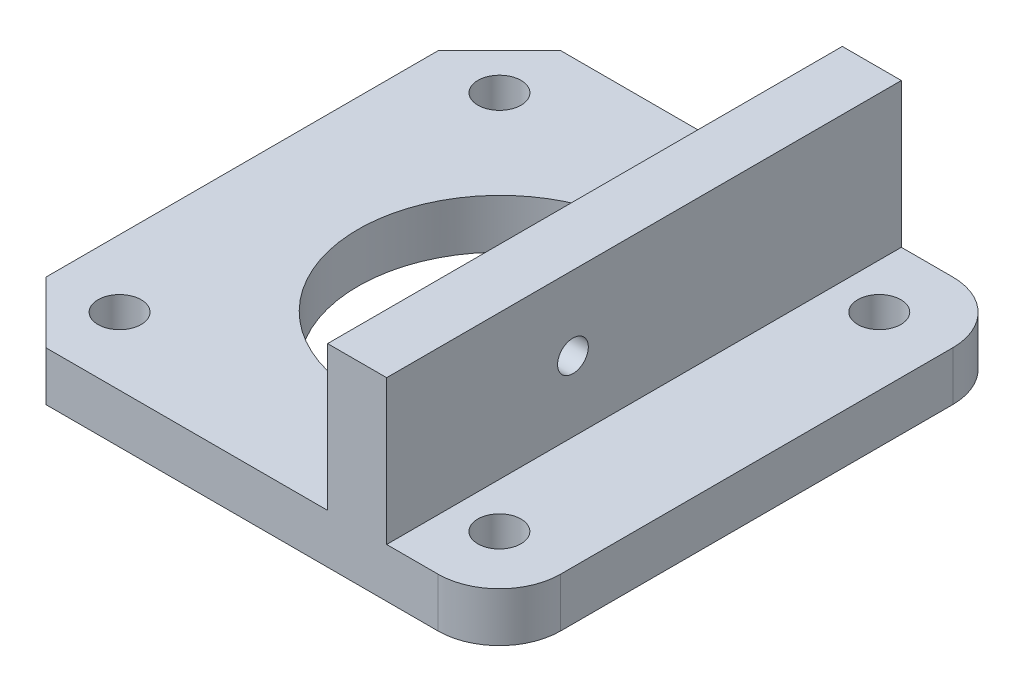
SolidWorks part; units mm, degrees
ref_plane "Front Plane" through (0, 0, 0) normal (0, 0, 1) x (1, 0, 0)
ref_plane "Top Plane" through (0, 0, 0) normal (0, 1, 0) x (1, 0, 0)
ref_plane "Right Plane" through (0, 0, 0) normal (1, 0, 0) x (0, 0, -1)
sketch "Sketch2" plane through (0, 0, 0) normal (0, 1, 0) x (1, 0, 0)
  line L0 (0, 0) -> (0, 24.9167) construction
  line L1 (-41.6298, 0) -> (51.2581, 0) construction
  line L2 (4.04, 20.9) -> (4.04, -21.11) construction
  line L3 (-20.96, 20.9) -> (21.04, 20.9)
  line L4 (-20.96, 20.9) -> (-20.96, -21.11)
  line L5 (-20.96, -21.11) -> (21.04, -21.11)
  line L6 (21.04, 20.9) -> (21.04, -21.11)
  line L7 (11.29, 33.2748) -> (11.29, -21.11) construction
  line L8 (2.0234, 16.1611) -> (2.0234, 11.4222)
  line L9 (2.0234, 16.1611) -> (4.04, 16.1611)
  line L10 (4.04, 16.1611) -> (11.29, 16.1611)
  line L11 (11.29, 16.1611) -> (11.29, 2.6638)
  arc A0 (2.0234, 11.4222) -> (11.29, 2.6638) centre (0, 0) ccw
  dimension "D5" = 17
  dimension "D1" = 21.11
  dimension "D2" = 21.04
  dimension "D3" = 20.96
  dimension "D4" = 20.9
  dimension "D6" = 9.75
extrude "Boss-Extrude2" add sketch "Sketch2" along normal blind 4.02
sketch "Sketch3" plane through (0, 0, 21.11) normal (0, 0, 1) x (1, 0, 0)
  line L0 (-20.96, 0) -> (21.04, 0) construction
  line L2 (7.0232, 0) -> (11.8432, 0)
  line L3 (7.0232, 0) -> (7.0232, 15.81)
  line L4 (7.0232, 15.81) -> (11.8432, 15.81)
  line L5 (11.8432, 0) -> (11.8432, 15.81)
  dimension "D1" = 15.81
  dimension "D2" = 4.82
extrude "Boss-Extrude3" add sketch "Sketch3" against normal blind 42.01 contours L3 L2 L5 L4
sketch "Sketch4" plane through (0, 0, 0) normal (0, -1, 0) x (1, 0, 0)
  circle A0 centre (0, 0) radius 11.6
extrude "Cut-Extrude1" cut sketch "Sketch4" against normal blind 4.02
sketch "Sketch5" plane through (11.8432, 0, 0) normal (1, 0, 0) x (0, 0, -1)
  line L0 (-21.11, 4.02) -> (-21.11, 15.81) construction
  circle A0 centre (-5.905, 9.7519) radius 1.255
  dimension "D1" = 15.205
extrude "Cut-Extrude2" cut sketch "Sketch5" against normal through all
chamfer "Chamfer1" distance 5 angle 45 2 edges at (-20.96, 2.01, -20.9) (-20.96, 2.01, 21.11)
sketch "Sketch6" plane through (0, 4.02, 0) normal (0, 1, 0) x (1, 0, 0)
  line L0 (7.0232, 20.9) -> (-15.96, 20.9) construction
  line L1 (21.04, 20.9) -> (11.8432, 20.9) construction
  line L2 (21.04, -21.11) -> (21.04, 20.9) construction
  line L3 (-20.96, 15.9) -> (-20.96, -16.11) construction
  circle A0 centre (-15.48, 15.42) radius 1.76
  circle A1 centre (15.52, 15.42) radius 1.76
  circle A2 centre (-15.48, -15.5859) radius 1.76
  circle A3 centre (15.52, -15.5859) radius 1.76
  dimension "D1" = 5.48
  dimension "D2" = 5.48
  dimension "D3" = 5.52
  dimension "D4" = 5.48
  dimension "D5" = 31.0059
extrude "Cut-Extrude3" cut sketch "Sketch6" against normal blind 4.02
fillet "Fillet1" radius 5 2 edges at (21.04, 2.01, 21.11) (21.04, 2.01, -20.9)
sketch "Sketch7" plane through (7.0232, 0, 0) normal (-1, 0, 0) x (0, 0, 1)
  circle A0 centre (-13.937, 9.4803) radius 2.515
  point P2 (-13.937, 9.4803)
extrude "Boss-Extrude4" add sketch "Sketch7" along normal blind 3.92
fillet "Fillet3" radius 0.5 1 edges at (3.1032, 6.9653, -13.937)
